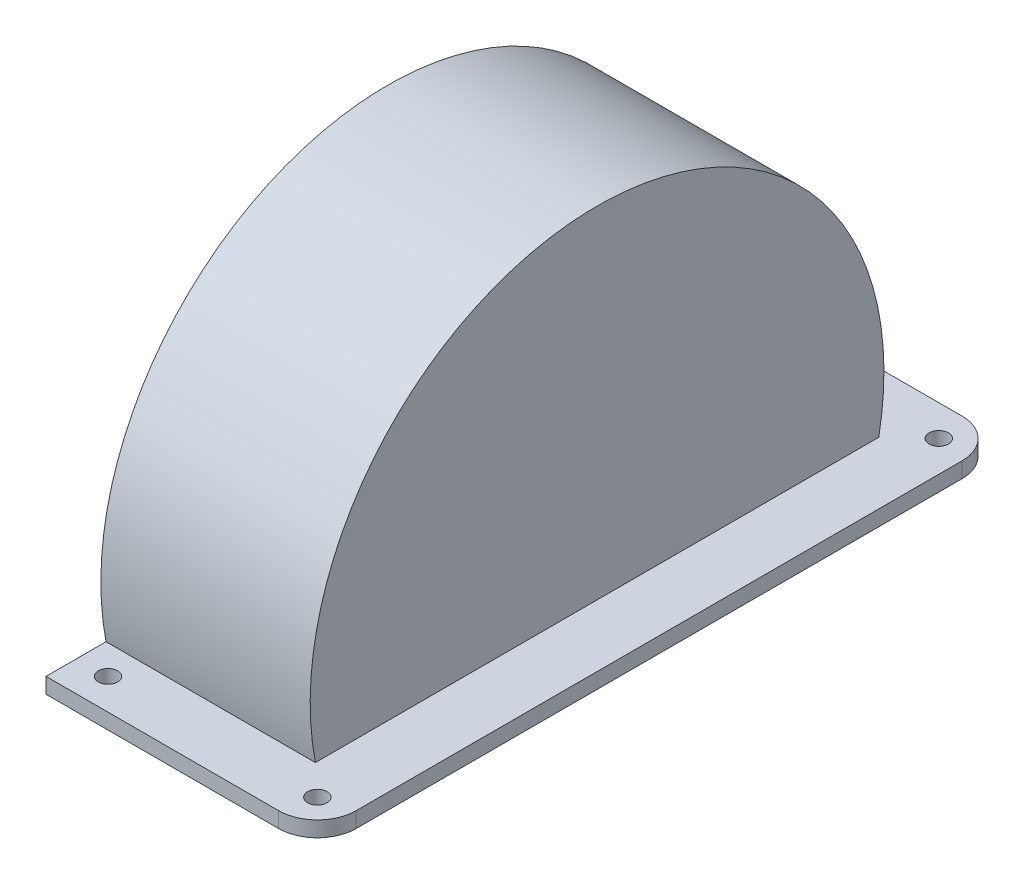
SolidWorks part; units mm, degrees
ref_plane "Front Plane" through (0, 0, 0) normal (0, 0, 1) x (1, 0, 0)
ref_plane "Top Plane" through (0, 0, 0) normal (0, 1, 0) x (1, 0, 0)
ref_plane "Right Plane" through (0, 0, 0) normal (1, 0, 0) x (0, 0, -1)
sketch "Sketch1" plane through (0, 0, 0) normal (1, 0, 0) x (0, 0, -1)
  line L0 (-36.1248, -8) -> (36.1248, -8)
  circle A0 centre (0, 0) radius 32 construction
  arc A1 (36.1248, -8) -> (-36.1248, -8) centre (0, 0) ccw
  dimension "D1" = 64
  dimension "D2" = 74
  dimension "D3" = 8
extrude "Boss-Extrude1" add sketch "Sketch1" along normal mid plane 29
shell "Shell1" thickness 2
sketch "Sketch3" plane through (0, -8, 0) normal (0, -1, 0) x (1, 0, 0)
  line L5 (-12.5, -34.0735) -> (12.5, -34.0735)
  line L6 (-12.5, -34.0735) -> (-12.5, 34.0735)
  line L7 (-12.5, 34.0735) -> (12.5, 34.0735)
  line L8 (12.5, -34.0735) -> (12.5, 34.0735)
  line L9 (-12.5, -34.0735) -> (12.5, 34.0735) construction
  line L10 (-12.5, 34.0735) -> (12.5, -34.0735) construction
  line L14 (-9.5, 44.0735) -> (17.5, 44.0735)
  line L15 (22.5, -39.0735) -> (22.5, 39.0735)
  line L16 (-9.5, -44.0735) -> (17.5, -44.0735)
  line L22 (-14.5, 39.0735) -> (-14.5, -39.0735)
  line L23 (-22.5, 44.0735) -> (22.5, 44.0735) construction
  line L24 (-22.5, -44.0735) -> (-22.5, 44.0735) construction
  line L25 (-22.5, -44.0735) -> (22.5, -44.0735) construction
  line L26 (22.5, -44.0735) -> (22.5, 44.0735) construction
  line L27 (-9.5, 44.0735) -> (-14.5, 44.0735)
  line L28 (-14.5, 44.0735) -> (-14.5, 39.0735)
  line L29 (-9.5, -44.0735) -> (-14.5, -44.0735)
  line L30 (-14.5, -44.0735) -> (-14.5, -39.0735)
  circle A0 centre (18.5, 40.0735) radius 1.25
  circle A1 centre (-8.5, 40.0735) radius 1.25
  circle A2 centre (18.5, -40.0735) radius 1.25
  circle A3 centre (-8.5, -40.0735) radius 1.25
  arc A5 (22.5, -39.0735) -> (17.5, -44.0735) centre (17.5, -39.0735) cw
  arc A7 (17.5, 44.0735) -> (22.5, 39.0735) centre (17.5, 39.0735) cw
  point P0 (0, 0)
  dimension "D4" = 2.5
  dimension "D2" = 4
  dimension "D3" = 4
  dimension "D5" = 6
  dimension "D6" = 4
  dimension "D1" = 10
extrude "Boss-Extrude2" add sketch "Sketch3" along normal mid plane 2
sketch "Sketch4" plane through (-12.5, 0, 0) normal (1, 0, 0) x (0, 0, -1)
  line L0 (-44.0735, -7) -> (-36.3318, -7)
  line L1 (44.0735, -7) -> (44.0735, -9)
  line L2 (44.0735, -9) -> (-44.0735, -9)
  line L3 (-44.0735, -9) -> (-44.0735, -7)
  line L4 (36.3318, -7) -> (44.0735, -7)
  arc A0 (36.3318, -7) -> (-36.3318, -7) centre (0, 0) ccw
extrude "Cut-Extrude1" cut sketch "Sketch4" against normal blind 2
